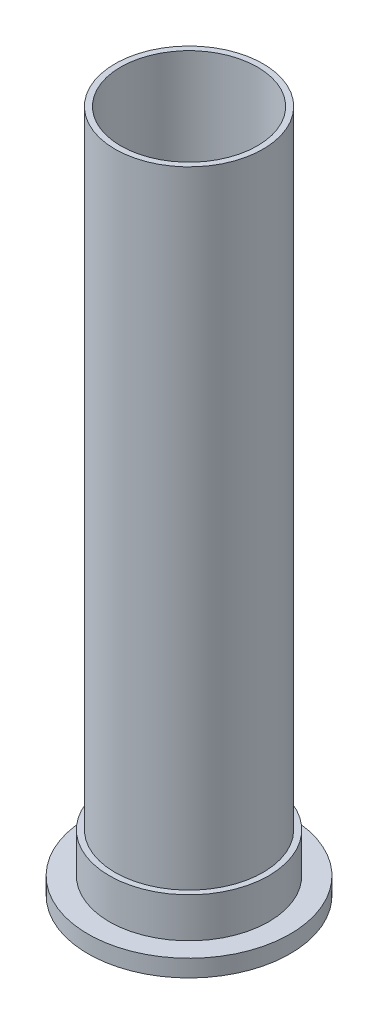
SolidWorks part; units mm, degrees
material "7075-T6 (SN)"
ref_plane "Front Plane" through (0, 0, 0) normal (0, 0, 1) x (1, 0, 0)
ref_plane "Top Plane" through (0, 0, 0) normal (0, 1, 0) x (1, 0, 0)
ref_plane "Right Plane" through (0, 0, 0) normal (1, 0, 0) x (0, 0, -1)
sketch "Sketch2" plane through (0, 0, 0) normal (0, 1, 0) x (1, 0, 0)
  circle A0 centre (0, 0) radius 38.1
  circle A1 centre (0, 0) radius 41.275
  dimension "D1" = 82.55
  dimension "D2" = 76.2
extrude "Base Cylinder" add sketch "Sketch2" along normal blind 381
sketch "Sketch3" plane through (0, 0, 0) normal (0, -1, 0) x (1, 0, 0)
  circle A0 centre (0, 0) radius 38.1
  circle A1 centre (0, 0) radius 56.3562
  dimension "D1" = 112.7125
extrude "Aft Flange" add sketch "Sketch3" against normal blind 9.525
sketch "Sketch34" plane through (0, 0, 0) normal (0, -1, 0) x (1, 0, 0)
  circle A0 centre (0, 0) radius 39.75
  dimension "D1" = 79.5
extrude "TemperatureInsert" cut sketch "Sketch34" against normal blind 28.575
sketch "Sketch6" plane through (0, 0, 0) normal (0, -1, 0) x (1, 0, 0)
  circle A0 centre (0, 0) radius 46.9011
  circle A1 centre (0, 0) radius 44.2849
  dimension "D1" = 93.8022
  dimension "D2" = 88.5698
extrude "Aft O-Ring" [suppressed] cut sketch "Sketch6" against normal blind 1.9812
sketch "Sketch33" plane through (0, 9.525, 0) normal (0, 1, 0) x (1, 0, 0)
  circle A0 centre (0, 0) radius 41.275
  circle A1 centre (0, 0) radius 44.45
  dimension "D1" = 82.55
  dimension "D2" = 88.9
extrude "CriticalBoss" add sketch "Sketch33" along normal blind 22.225
sketch "Sketch For Bolt Holes" plane through (0, 0, 0) normal (0, -1, 0) x (1, 0, 0)
  circle A0 centre (-51.6255, 0) radius 1.5875
  circle A1 centre (-44.709, 25.8128) radius 1.5875
  circle A2 centre (-25.8128, 44.709) radius 1.5875
  circle A3 centre (0, 51.6255) radius 1.5875
  circle A4 centre (25.8127, 44.709) radius 1.5875
  circle A5 centre (44.709, 25.8128) radius 1.5875
  circle A6 centre (51.6255, 0) radius 1.5875
  circle A7 centre (44.709, -25.8127) radius 1.5875
  circle A8 centre (25.8128, -44.709) radius 1.5875
  circle A9 centre (0, -51.6255) radius 1.5875
  circle A10 centre (-25.8127, -44.709) radius 1.5875
  circle A11 centre (-44.709, -25.8128) radius 1.5875
  point P36 (0, 0)
  dimension "D2" = 3.175
  dimension "D1" = 51.6255
  dimension "D3" = 12
hole_wizard "Bolt Circle" [suppressed] positions "Sketch8" profile "Sketch9" hole size "#4-40" standard "ANSI Inch"
sketch "Sketch8" plane through (0, 0, 0) normal (0, -1, 0) x (-1, 0, 0)
  point P0 (-25.8127, -44.709)
  point P3 (-44.709, -25.8128)
  point P6 (-51.6255, 0)
  point P9 (-44.709, 25.8127)
  point P12 (-25.8128, 44.709)
  point P15 (0, 51.6255)
  point P18 (25.8127, 44.709)
  point P21 (44.709, 25.8128)
  point P24 (51.6255, 0)
  point P27 (44.709, -25.8128)
  point P30 (25.8128, -44.709)
  point P33 (0, -51.6255)
  point P36 (-25.8127, -44.709)
  point P38 (-44.709, -25.8128)
  point P40 (-51.6255, 0)
sketch "Sketch9" plane through (25.8127, 0, 44.709) normal (1, 0, 0) x (0, 0, -1)
  line L0 (0, 0) -> (0, 9.525)
  line L1 (0, 9.525) -> (1.1303, 9.525)
  line L2 (1.1303, 9.525) -> (1.1303, 0)
  line L5 (1.1303, 0) -> (0, 0)
  line L11 (0, -6.35) -> (0, 107.95) construction
  dimension "Thru Hole Dia." = 2.2606
  dimension "Thru Hole Depth" = 9.525
sketch "Dowel Hole Sketch" [suppressed] plane through (0, 0, 0) normal (0, -1, 0) x (1, 0, 0)
  line L0 (0, 0) -> (-51.6255, 0) construction
  line L1 (0, 0) -> (-49.8664, -13.3617) construction
  line L2 (0, 0) -> (0, -51.6255) construction
  line L3 (0, 0) -> (49.8664, 13.3617) construction
  circle A0 centre (0, 0) radius 51.6255
  circle A1 centre (-49.8664, -13.3617) radius 4.6172
  circle A2 centre (49.8664, 13.3617) radius 3.4532
  dimension "D1" = 15
hole_wizard "Hole1" [suppressed] positions "Sketch14" profile "Sketch12" legacy
sketch "Sketch14" [suppressed] plane through (0, 0, 0) normal (0, -1, 0) x (-1, 0, 0)
  point P0 (49.8664, 13.3617)
  point P3 (-49.8664, -13.3617)
sketch "Sketch12" plane through (-49.8664, 0, -13.3617) normal (1, 0, 0) x (0, 0, -1)
  line L0 (0, 0) -> (0, 9.525)
  line L1 (0, 9.525) -> (1.1906, 9.525)
  line L2 (1.1906, 9.525) -> (1.1906, 4.7625)
  line L3 (1.1906, 4.7625) -> (2.3813, 4.7625)
  line L4 (2.3813, 4.7625) -> (2.3813, 0)
  line L5 (2.3813, 0) -> (0, 0)
  line L6 (0, 110) -> (0, -10) construction
  dimension "Diameter" = 2.3813
  dimension "Depth" = 9.525
  dimension "C-Bore Diameter" = 4.7625
  dimension "C-Bore Depth" = 4.7625
ref_plane "Hoop Mid-Plane" through (0, 190.5, 0) normal (0, 1, 0) x (1, 0, 0)
ref_plane "PressureTapHolePlane" through (0, 0, 44.45) normal (0, 0, 1) x (1, 0, 0)
ref_plane "TemperatureTapPlane" through (0, 0, -44.45) normal (0, 0, 1) x (1, 0, 0)
sketch "ThermoHole" plane through (0, 0, -44.45) normal (0, 0, 1) x (1, 0, 0)
  line L0 (-56.3562, 0) -> (56.3562, 0) construction
  circle A0 centre (0, 19.05) radius 3.175
  dimension "D1" = 19.05
  dimension "D2" = 6.35
sketch "Sketch35" plane through (0, 0, 44.45) normal (0, 0, 1) x (1, 0, 0)
  line L0 (-56.3562, 0) -> (56.3562, 0) construction
  circle A0 centre (0, 19.05) radius 1.5875
  dimension "D1" = 19.05
  dimension "D2" = 3.175
extrude "Pressure Tap Aft Big" [suppressed] cut sketch "Sketch35" against normal blind 2.3813
sketch "Sketch41" [suppressed] plane through (0, 0, 42.0687) normal (0, 0, 1) x (1, 0, 0)
  circle A0 centre (0, 19.05) radius 0.1984
extrude "Pressure Tap Aft Small" [suppressed] cut sketch "Sketch41" against normal up to next
hole_wizard "1/8 NPT Tapped ThermocoupleHole" [suppressed] positions "Sketch43" profile "Sketch44" size "1/8" standard "ANSI Inch"
sketch "Sketch43" plane through (0, 0, -44.45) normal (0, 0, 1) x (1, 0, 0)
  point P0 (0, 19.05)
sketch "Sketch44" plane through (0, 19.05, -44.45) normal (1, 0, 0) x (0, 1, 0)
  line L0 (0, 0) -> (0, 14.2175)
  line L1 (4.2164, 11.684) -> (0, 14.2175)
  line L2 (-4.2164, 11.684) -> (0, 14.2175) construction
  line L3 (4.2164, 11.684) -> (4.2164, 6.858)
  line L4 (4.2164, 6.858) -> (4.9362, 6.858)
  line L5 (4.9362, 6.858) -> (5.1415, 0)
  line L6 (-4.9362, 6.858) -> (-5.1415, 0) construction
  line L7 (5.1415, 0) -> (0, 0)
  line L8 (0, -6.35) -> (0, 107.95) construction
  line L11 (-4.2164, 6.858) -> (-4.9362, 6.858) construction
  dimension "Tap Drill Dia." = 8.4328
  dimension "Tap Drill Depth" = 11.684
  dimension "Thread Dia." = 10.283
  dimension "Thread Angle" = 3.43
  dimension "Thread Depth" = 6.858
  dimension "Drill Angle" = 118
